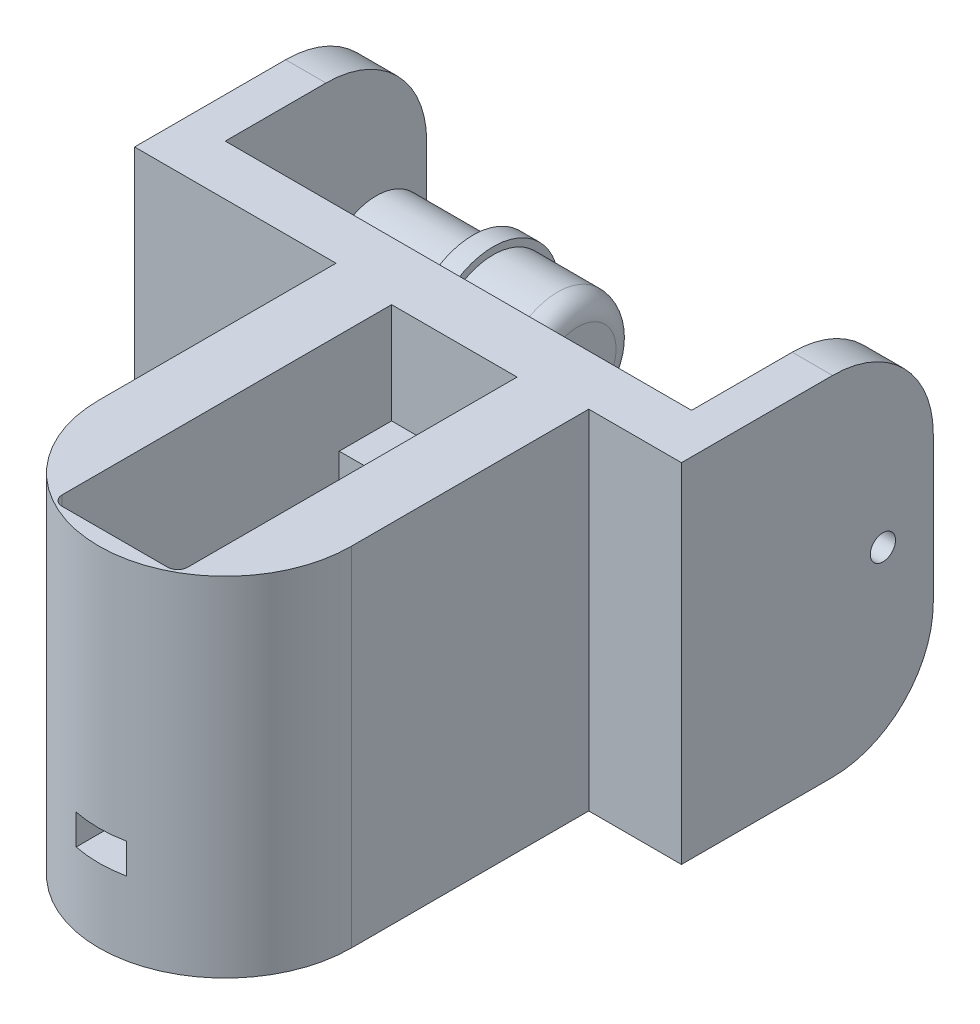
SolidWorks part; units mm, degrees
ref_plane "Front Plane" through (0, 0, 0) normal (0, 0, 1) x (1, 0, 0)
ref_plane "Top Plane" through (0, 0, 0) normal (0, 1, 0) x (1, 0, 0)
ref_plane "Right Plane" through (0, 0, 0) normal (1, 0, 0) x (0, 0, -1)
sketch "Sketch4" plane through (0, 0, 0) normal (0, 0, 1) x (1, 0, 0)
  line L1 (-6.23, -9.975) -> (6.23, -9.975)
  line L2 (-6.23, -9.975) -> (-6.23, 7.275)
  line L3 (-6.23, 7.275) -> (6.23, 7.275)
  line L4 (6.23, -9.975) -> (6.23, 7.275)
  point P4 (0, 7.275)
  dimension "D1" = 12.46
  dimension "D2" = 17.25
  dimension "D3" = 9.975
extrude "Boss-Extrude3" add sketch "Sketch4" along normal blind 6
sketch "Sketch8" plane through (0, -9.975, 0) normal (0, -1, 0) x (-1, 0, 0)
  circle A0 centre (0, -23.55) radius 12.5468
  circle A1 centre (0, -23.55) radius 11.15
  dimension "D1" = 22.3
  dimension "D2" = 23.55
extrude "Boss-Extrude6" add sketch "Sketch8" along normal blind 7.3 and the other way up to surface (17.25 mm away) other way up to face at (0, 7.275, 3)
sketch "Sketch5" plane through (0, 7.275, 0) normal (0, 1, 0) x (1, 0, 0)
  line L8 (12.5468, -23.55) -> (12.5468, 0)
  line L9 (12.5468, 0) -> (6.23, 0)
  line L10 (-12.5468, -23.55) -> (-12.5468, 0)
  line L11 (-12.5468, 0) -> (-6.23, 0)
  line L12 (-6.23, 0) -> (-6.23, -29.7)
  line L14 (6.23, -29.7) -> (6.23, 0)
  line L15 (-6.23, -29.7) -> (6.23, -29.7)
  line L16 (6.23, -6) -> (-6.23, -6) construction
  circle A0 centre (0, -23.55) radius 12.5468 construction
  arc A1 (-12.5468, -23.55) -> (12.5468, -23.55) centre (0, -23.55) ccw
  dimension "D1" = 23.7
  dimension "D2" = 23.55
extrude "Boss-Extrude4" add sketch "Sketch5" against normal up to surface (17.25 mm away) up to face at (0, -9.975, 3)
sketch "Sketch6" plane through (0, 7.275, 0) normal (0, 1, 0) x (1, 0, 0)
  line L0 (6.23, -6) -> (-6.23, -6) construction
  line L3 (6.23, -29.7) -> (-6.23, -29.7) construction
  circle A0 centre (0, -3.6) radius 0.5
  circle A1 centre (0, -32.1) radius 0.5
  dimension "D1" = 1
  dimension "D3" = 1
  dimension "D2" = 2.4
  dimension "D4" = 2.4
extrude "Cut-Extrude1" cut sketch "Sketch6" against normal blind 15
chamfer "Chamfer1" distance 0.5 angle 60 2 edges at (0, 7.275, 4.1) (0, 7.275, 32.6)
sketch "Sketch10" plane through (0, 7.275, 0) normal (0, 1, 0) x (1, 0, 0)
  line L1 (-6.23, -6) -> (6.23, -6)
  line L2 (-6.23, -6) -> (-6.23, -29.7)
  line L3 (-6.23, -29.7) -> (6.23, -29.7)
  line L4 (6.23, -6) -> (6.23, -29.7)
extrude "Cut-Extrude3" cut sketch "Sketch10" against normal up to surface (17.25 mm away) up to face at (0, -9.975, 27.1007)
ref_plane "Plane1" through (0, 0, 36.0968) normal (0, 0, 1) x (1, 0, 0)
sketch "Sketch11" plane through (0, 0, 36.0968) normal (0, 0, 1) x (1, 0, 0)
  line L0 (-11.15, -9.975) -> (11.15, -9.975) construction
  line L1 (-2.5, -6.975) -> (2.5, -6.975)
  line L2 (-2.5, -6.975) -> (-2.5, -9.975)
  line L3 (-2.5, -9.975) -> (2.5, -9.975)
  line L4 (2.5, -6.975) -> (2.5, -9.975)
  point P4 (0, -6.975)
  dimension "D1" = 0
  dimension "D2" = 5
  dimension "D3" = 3
extrude "Cut-Extrude4" cut sketch "Sketch11" against normal up to next
sketch "Sketch13" plane through (0, -17.275, 0) normal (0, -1, 0) x (1, 0, 0)
  line L0 (-12.5468, 23.55) -> (-12.5468, 0)
  line L1 (-12.5468, 0) -> (12.5468, 0)
  line L2 (12.5468, 0) -> (12.5468, 23.55)
  arc A0 (-12.5468, 23.55) -> (12.5468, 23.55) centre (0, 23.55) ccw
  point P3 (0, 0)
extrude "Boss-Extrude7" add sketch "Sketch13" against normal up to surface (7.3 mm away) up to face at (-6.0145, -9.975, 27.3356)
sketch "Sketch15" plane through (0, 7.275, 0) normal (0, 1, 0) x (1, 0, 0)
  line L0 (-12.5468, 0) -> (12.5468, 0)
  line L1 (12.5468, 0) -> (12.5468, -23.55)
  line L2 (-12.5468, 0) -> (-12.5468, -23.55)
  line L3 (6.23, -6) -> (6.23, -29.7) construction
  line L4 (-6.23, -0.8) -> (6.23, -0.8)
  line L5 (-6.23, -0.8) -> (-6.23, -33.5)
  line L6 (-5.23, -34.5) -> (5.23, -34.5)
  line L7 (6.23, -0.8) -> (6.23, -33.5)
  arc A0 (-12.5468, -23.55) -> (12.5468, -23.55) centre (0, -23.55) ccw
  circle A1 centre (0, -3.6) radius 0.5 construction
  arc A2 (5.23, -34.5) -> (6.23, -33.5) centre (5.23, -33.5) ccw
  arc A3 (-6.23, -33.5) -> (-5.23, -34.5) centre (-5.23, -33.5) ccw
  point P15 (0, -0.8)
  dimension "D1" = 0.8
  dimension "D3" = 1
  dimension "D2" = 2.8
  dimension "D4" = 0
  dimension "D5" = 34.5
extrude "Boss-Extrude9" add sketch "Sketch15" along normal blind 10
sketch "Sketch20" plane through (0, -17.275, 0) normal (0, -1, 0) x (1, 0, 0)
  circle A0 centre (0, 23.55) radius 7.15
  circle A1 centre (0, 23.55) radius 11.15
  circle A2 centre (0, 23.55) radius 11.15 construction
  dimension "D1" = 14.3
extrude "Boss-Extrude11" add sketch "Sketch20" against normal up to surface (7.3 mm away) up to face at (-6.0145, -9.975, 27.3356)
sketch "Sketch21" plane through (0, -17.275, 0) normal (0, -1, 0) x (1, 0, 0)
  circle A0 centre (0, 23.55) radius 7.15
  circle A1 centre (0, 23.55) radius 10.15
  circle A2 centre (0, 23.55) radius 7.15 construction
  dimension "D1" = 20.3
extrude "Cut-Extrude7" cut sketch "Sketch21" against normal blind 1.3
sketch "Sketch17" plane through (0, 17.275, 0) normal (0, 1, 0) x (1, 0, 0)
  line L0 (21.75, 25) -> (21.75, 0)
  line L1 (21.75, 0) -> (-32.5468, 0)
  line L2 (-32.5468, 0) -> (-32.5468, 25)
  line L3 (-32.5468, 25) -> (-28.5468, 25)
  line L4 (-28.5468, 25) -> (-28.5468, 5)
  line L5 (-28.5468, 5) -> (17.75, 5)
  line L6 (17.75, 5) -> (17.75, 25)
  line L7 (17.75, 25) -> (21.75, 25)
  line L8 (-12.5468, -23.55) -> (-12.5468, 0) construction
  line L9 (12.5468, 0) -> (12.5468, -23.55) construction
  dimension "D1" = 4
  dimension "D2" = 5.2032
  dimension "D3" = 4
  dimension "D4" = 25
  dimension "D5" = 5
  dimension "D6" = 20
extrude "Boss-Extrude10" add sketch "Sketch17" against normal up to surface (34.55 mm away) up to face at (0, -17.275, 13.4)
sketch "Sketch18" plane through (17.75, 0, 0) normal (-1, 0, 0) x (0, 0, 1)
  line L0 (-25, -17.275) -> (-25, 17.275) construction
  line L1 (-25, 6.2191) -> (-5, 6.2191)
  line L2 (-25, 6.2191) -> (-25, -6.2191)
  line L3 (-25, -6.2191) -> (-5, -6.2191)
  line L4 (-5, 6.2191) -> (-5, -6.2191)
  line L5 (-5, -17.275) -> (-5, 17.275) construction
  point P6 (-25, 0)
  point P7 (-25, 0)
  dimension "D1" = 0
extrude "Cut-Extrude5" cut sketch "Sketch18" against normal blind 2
sketch "Sketch19" plane through (19.75, 0, 0) normal (-1, 0, 0) x (0, 0, 1)
  line L0 (-25, -17.275) -> (-25, 17.275) construction
  circle A0 centre (-20, 0) radius 1.25
  dimension "D1" = 2.5
  dimension "D2" = 5
extrude "Cut-Extrude6" cut sketch "Sketch19" against normal through all both and the other way through all
fillet "Fillet1" radius 10 4 edges at (19.75, 17.275, -25) (19.75, -17.275, -25) (-30.5468, -17.275, -25) (-30.5468, 17.275, -25)
ref_plane "Plane2" through (0, 0, 0) normal (1, 0, 0) x (0, 0, -1)
ref_plane "Plane3" through (0, 0, 0) normal (0, -1, 0) x (-1, 0, 0)
sketch "Sketch22" plane through (-28.5468, 0, 0) normal (1, 0, 0) x (0, 0, -1)
  circle A0 centre (20, 0) radius 5.8
  dimension "D1" = 11.6
extrude "Boss-Extrude12" add sketch "Sketch22" along normal blind 20
fillet "Fillet2" radius 2 1 edges at (-8.5468, 0, -25.8)
sketch "Sketch23" plane through (-28.5468, 0, 0) normal (1, 0, 0) x (0, 0, -1)
  circle A0 centre (20, 0) radius 5.08
  circle A1 centre (20, 0) radius 5.9309
  dimension "D1" = 10.16
extrude "Cut-Extrude8" cut sketch "Sketch23" along normal blind 11.6
sketch "Sketch24" plane through (-16.9468, 0, 0) normal (-1, 0, 0) x (0, 0, 1)
  circle A0 centre (-20, 0) radius 6.5
extrude "Boss-Extrude13" add sketch "Sketch24" along normal blind 2
sketch "Sketch25" plane through (-32.5468, 0, 0) normal (-1, 0, 0) x (0, 0, 1)
  circle A0 centre (-20, 0) radius 1.25
extrude "Boss-Extrude14" add sketch "Sketch25" against normal blind 2
sketch "Sketch26" plane through (-28.5468, 0, 0) normal (1, 0, 0) x (0, 0, -1)
  line L0 (5, -17.275) -> (5, 17.275) construction
  line L1 (5, -9.775) -> (10, -9.775)
  line L2 (5, -9.775) -> (5, -6.775)
  line L3 (5, -6.775) -> (10, -6.775)
  line L4 (10, -9.775) -> (10, -6.775)
  line L5 (0, -17.275) -> (15, -17.275) construction
  line L6 (5, -5.259) -> (10, -5.259)
  line L7 (5, -5.259) -> (5, -2.259)
  line L8 (5, -2.259) -> (10, -2.259)
  line L9 (10, -5.259) -> (10, -2.259)
  dimension "D1" = 1.516
  dimension "D2" = 3
  dimension "D3" = 3
  dimension "D4" = 0
  dimension "D5" = 5
  dimension "D6" = 7.5
extrude "Boss-Extrude15" add sketch "Sketch26" along normal blind 5
